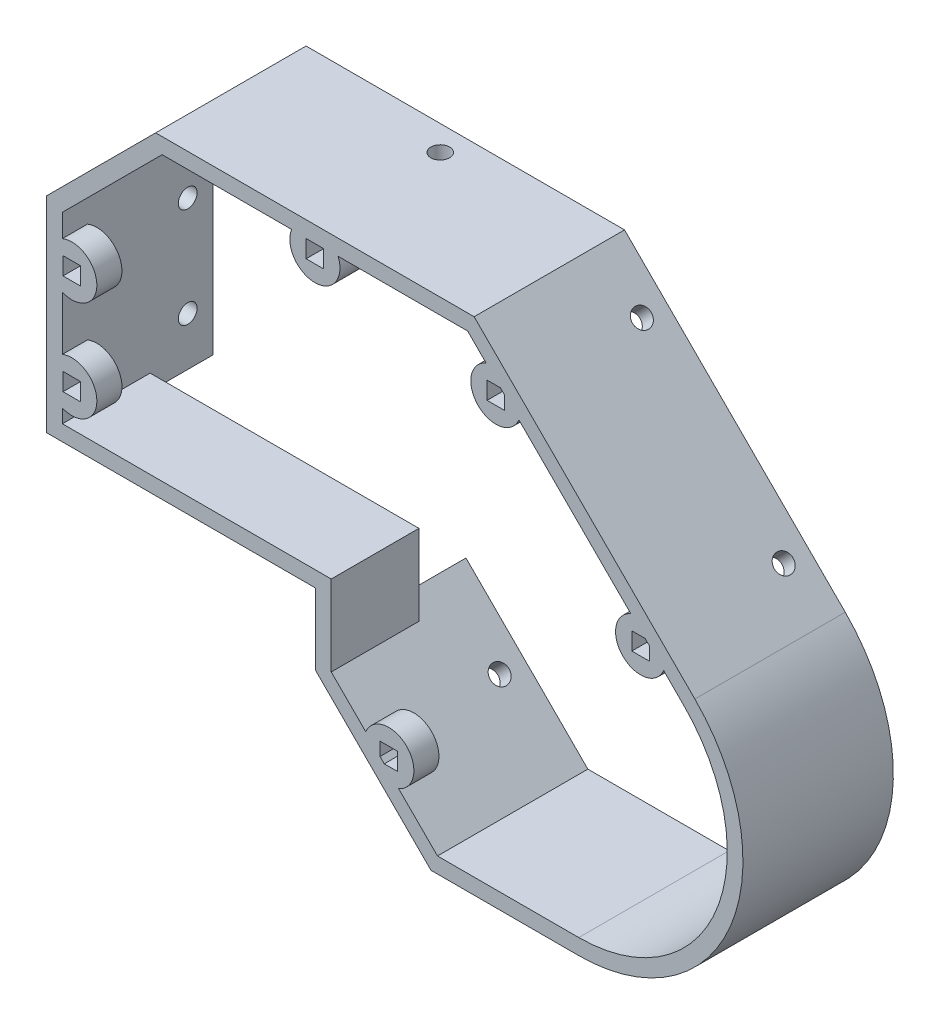
SolidWorks part; units mm, degrees
ref_plane "Plano frontal" through (0, 0, 0) normal (0, 0, 1) x (1, 0, 0)
ref_plane "Plano superior" through (0, 0, 0) normal (0, 1, 0) x (1, 0, 0)
ref_plane "Plano direito" through (0, 0, 0) normal (1, 0, 0) x (0, 0, -1)
sketch "Model" plane through (0, 0, 0) normal (0, 0, 1) x (1, 0, 0)
  line L0 (0, 0) -> (39, 0) construction
  line L1 (-0.7, 2.5) -> (39, 2.5)
  line L2 (39.7, 0) -> (39.7, -6.8548) construction
  line L3 (0, 0) -> (0, 31.4419) construction
  line L4 (50.1111, 46.949) -> (15.5071, 46.949) construction
  line L5 (0, 31.4419) -> (15.5071, 46.949) construction
  line L6 (42.2, -9.3548) -> (52.4452, -19.6) construction
  line L7 (39, -7.1448) -> (51.9502, -20.095) construction
  line L8 (97.9635, 12.6635) -> (63.6779, 46.949) construction
  line L9 (50.1111, 46.949) -> (63.6779, 46.949) construction
  line L10 (52.4452, -19.6) -> (59.4452, -26.6) construction
  line L11 (81.7, -26.6) -> (59.4452, -26.6) construction
  line L12 (-0.7, 0) -> (39, 0)
  line L13 (-0.7, 0) -> (-3.2, 0)
  line L14 (42.2, -10.3448) -> (51.9502, -20.095)
  line L15 (51.9502, -20.095) -> (59.1552, -27.3)
  line L16 (81.7, -27.3) -> (59.1552, -27.3)
  line L17 (98.4584, 13.1584) -> (63.9678, 47.649)
  line L18 (50.1111, 47.649) -> (63.9678, 47.649)
  line L19 (50.1111, 47.649) -> (15.2171, 47.649)
  line L20 (-0.7, 31.7319) -> (15.2171, 47.649)
  line L21 (-0.7, 2.5) -> (-0.7, 31.7319)
  line L22 (0, 0) -> (-0.7, 0) construction
  line L23 (38.8515, -10.5318) -> (50.1824, -21.8627) construction
  line L24 (-3.2, 0) -> (-3.2, 5)
  line L25 (-0.7, -0.7) -> (-0.7, 31.7319) construction
  line L26 (-0.7, -0.7) -> (39, -0.7) construction
  line L27 (39, -0.7) -> (39, -7.1448) construction
  line L28 (39, -0.7) -> (39, -0.7) construction
  line L29 (39, 0) -> (39.7, 0)
  line L30 (39.7, 0) -> (39.7, -11.3803)
  line L31 (39, 2.5) -> (39.7, 2.5)
  line L32 (39.7, 2.5) -> (42.2, 2.5)
  line L33 (39, 0) -> (39.7, 0) construction
  line L34 (42.2, 2.5) -> (42.2, -10.3448)
  line L35 (-3.2, 5) -> (-3.2, 32.7674)
  line L36 (-3.2, 32.7674) -> (14.1816, 50.149)
  line L37 (50.1111, 50.149) -> (14.1816, 50.149)
  line L38 (50.1111, 50.149) -> (65.0034, 50.149)
  line L39 (100.2262, 14.9262) -> (65.0034, 50.149)
  line L40 (81.7, -29.8) -> (58.1197, -29.8)
  line L41 (50.1824, -21.8627) -> (58.1197, -29.8)
  line L42 (39.7, -11.3803) -> (50.1824, -21.8627)
  line L43 (-0.7, 2.5) -> (-5.7, 2.5) construction
  line L44 (-5.7, 0) -> (-5.7, 2.5) construction
  line L45 (-0.7, 0) -> (-5.7, 0) construction
  line L46 (-3.2, 5) -> (-8.2, 5) construction
  line L47 (-8.2, -2.5) -> (-8.2, 5) construction
  line L48 (-0.7, -2.5) -> (39, -2.5) construction
  line L49 (-0.7, -2.5) -> (-8.2, -2.5) construction
  line L51 (40.6192, -8.764) -> (51.9502, -20.095) construction
  line L52 (39.7, -6.8548) -> (52.4452, -19.6) construction
  arc A0 (81.7, -27.3) -> (98.4584, 13.1584) centre (81.7, -3.6) ccw
  arc A1 (81.7, -29.8) -> (100.2262, 14.9262) centre (81.7, -3.6) ccw
  circle A2 centre (59.0726, 19.0274) radius 7.35 construction
  arc A5 (81.7, -26.6) -> (97.9635, 12.6635) centre (81.7, -3.6) ccw construction
  circle A6 centre (81.7, -3.6) radius 7.3 construction
  circle A13 centre (27.384, 23.481) radius 7.35 construction
  dimension "D2" = 2.5
  dimension "D1" = 0.7
extrude "Ressalto-extrusão1" add sketch "Model" along normal blind 48
sketch "Esboço12" plane through (57.5762, 57.5762, 0) normal (0.7071, 0.7071, 0) x (0, 0, -1)
  line L0 (-48, -35.4099) -> (-44, -35.4099) construction
  line L1 (-48, -60.3162) -> (-48, -10.5036) construction
  line L2 (-44, -35.4099) -> (-44, -43.4099) construction
  line L7 (-45.4, -52.0727) -> (-44, -52.0727) construction
  line L9 (-45.4, -20.0727) -> (-44, -20.0727) construction
  circle A0 centre (-44, -20.0727) radius 1.5
  circle A1 centre (-44, -52.0727) radius 1.5
extrude "Corte-extrusão10" cut sketch "Esboço12" against normal blind 10
sketch "Esboço13" plane through (0, 50.149, 0) normal (0, 1, 0) x (1, 0, 0)
  line L0 (39.5925, -48) -> (39.5925, -44) construction
  line L1 (65.0034, -48) -> (14.1816, -48) construction
  circle A0 centre (39.5925, -44) radius 1.5
extrude "Corte-extrusão11" cut sketch "Esboço13" against normal blind 10
sketch "Esboço14" plane through (-3.2, 0, 0) normal (-1, 0, 0) x (0, 0, 1)
  line L0 (48, 16.3837) -> (44, 16.3837) construction
  line L1 (48, 32.7674) -> (48, 0) construction
  line L2 (45.3801, 22.301) -> (45.3801, 25.101) construction
  line L3 (45.3626, 6.3583) -> (45.3626, 9.1235) construction
  line L4 (45.3801, 22.301) -> (45.3801, 25.101) construction
  line L5 (45.3626, 6.3583) -> (45.3626, 9.1235) construction
  line L6 (45.3801, 23.701) -> (44, 23.701) construction
  line L7 (45.3626, 7.7409) -> (44, 7.7409) construction
  circle A0 centre (44, 23.701) radius 1.5
  circle A1 centre (44, 7.7409) radius 1.5
extrude "Corte-extrusão12" cut sketch "Esboço14" against normal blind 10
sketch "Esboço15" plane through (14.1598, 14.1598, 0) normal (-0.7071, -0.7071, 0) x (0, 0, 1)
  line L0 (48, -62.1686) -> (44, -62.1686) construction
  line L1 (48, -62.1686) -> (0, -62.1686) construction
  line L2 (0, -36.4548) -> (0, -50.9436) construction
  line L3 (0, -50.9436) -> (0, -60.8431) construction
  line L4 (0, -36.4548) -> (0, -50.9436) construction
  line L5 (0, -50.9436) -> (0, -60.8431) construction
  line L6 (0, -60.8431) -> (0, -36.4548) construction
  line L7 (0, -36.4548) -> (0, -48.6489) construction
  line L8 (0, -48.6489) -> (48, -48.6489) construction
  line L9 (48, -36.1192) -> (48, -62.1686) construction
  line L11 (45.4, -48.2812) -> (45.4, -45.4812) construction
  line L12 (45.4, -48.2812) -> (45.4, -45.4812) construction
  line L13 (45.4, -46.8812) -> (44, -46.8812) construction
  circle A0 centre (44, -46.8812) radius 1.5
extrude "Corte-extrusão13" cut sketch "Esboço15" against normal blind 10
sketch "Esboço16" plane through (0, 0, 48) normal (0, 0, 1) x (1, 0, 0)
  line L0 (39.7, 0) -> (39.7, -7.8448)
  line L3 (42.2, -10.3448) -> (39.7, -7.8448)
  line L4 (42.2, -10.3448) -> (42.2, 2.5)
  line L5 (42.2, 2.5) -> (-0.7, 2.5)
  line L6 (39.7, 0) -> (39.7, -7.8448) construction
  line L12 (-0.7, 0) -> (39.7, 0)
  line L13 (-0.7, 2.5) -> (-0.7, 0)
extrude "Corte-extrusão14" cut sketch "Esboço16" against normal blind 10
sketch "Esboço18" plane through (0, 0, 0) normal (0, 0, -1) x (-1, 0, 0)
  line L8 (-39.7, 0) -> (3.2, 0)
  line L9 (3.2, 0) -> (3.2, 32.7674)
  line L10 (3.2, 32.7674) -> (-14.1816, 50.149)
  line L11 (-14.1816, 50.149) -> (-65.0034, 50.149)
  line L12 (-65.0034, 50.149) -> (-100.2262, 14.9262)
  line L13 (-81.7, -29.8) -> (-58.1197, -29.8)
  line L14 (-58.1197, -29.8) -> (-39.7, -11.3803)
  line L15 (-39.7, -11.3803) -> (-39.7, 0)
  line L16 (-39.7, 0) -> (3.2, 0)
  line L17 (3.2, 0) -> (3.2, 32.7674)
  line L18 (3.2, 32.7674) -> (-14.1816, 50.149)
  line L19 (-14.1816, 50.149) -> (-65.0034, 50.149)
  line L20 (-65.0034, 50.149) -> (-100.2262, 14.9262)
  line L21 (-81.7, -29.8) -> (-58.1197, -29.8)
  line L22 (-58.1197, -29.8) -> (-39.7, -11.3803)
  line L23 (-39.7, -11.3803) -> (-39.7, 0)
  arc A1 (-100.2262, 14.9262) -> (-81.7, -29.8) centre (-81.7, -3.6) ccw
  arc A2 (-100.2262, 14.9262) -> (-81.7, -29.8) centre (-81.7, -3.6) ccw
  dimension "D1" = 0
extrude "Corte-extrusão15" cut sketch "Esboço18" against normal blind 24
sketch "Esboço17" plane through (0, 0, 24) normal (0, 0, -1) x (-1, 0, 0)
  line L0 (-93.3365, 21.8159) -> (-95.4578, 19.6946) construction
  line L1 (-93.3365, 21.8159) -> (-95.4578, 19.6946) construction
  line L2 (-70.709, 44.4433) -> (-72.8304, 42.322) construction
  line L3 (-70.709, 44.4433) -> (-72.8304, 42.322) construction
  line L4 (-38.0925, 50.149) -> (-41.0925, 50.149) construction
  line L5 (-38.0925, 50.149) -> (-41.0925, 50.149) construction
  line L6 (3.2, 22.201) -> (3.2, 25.201) construction
  line L7 (3.2, 22.201) -> (3.2, 25.201) construction
  line L8 (3.2, 6.2409) -> (3.2, 9.2409) construction
  line L9 (3.2, 6.2409) -> (3.2, 9.2409) construction
  line L10 (-48.3705, -20.0508) -> (-46.2492, -17.9295) construction
  line L11 (-48.3705, -20.0508) -> (-46.2492, -17.9295) construction
  line L12 (-94.3971, 20.7553) -> (-91.5687, 17.9268) construction
  line L14 (-39.5925, 50.149) -> (-39.5925, 46.149) construction
  line L18 (-69.8727, 39.6229) -> (-67.0727, 39.6229)
  line L19 (-92.9687, 19.3268) -> (-90.1687, 19.3268)
  line L20 (-92.9687, 19.3268) -> (-92.9687, 16.5268)
  line L21 (-92.9687, 16.5268) -> (-90.1687, 16.5268)
  line L22 (-90.1687, 19.3268) -> (-90.1687, 16.5268)
  line L23 (-92.9687, 19.3268) -> (-90.1687, 16.5268) construction
  line L24 (-92.9687, 16.5268) -> (-90.1687, 19.3268) construction
  line L25 (-69.8727, 39.6229) -> (-67.0727, 42.4229) construction
  line L26 (-69.8727, 42.4229) -> (-67.0727, 39.6229) construction
  line L27 (-69.8727, 42.4229) -> (-69.8727, 39.6229)
  line L28 (-69.8727, 42.4229) -> (-67.0727, 42.4229)
  line L29 (-67.0727, 42.4229) -> (-67.0727, 39.6229)
  line L30 (-38.1925, 47.549) -> (-38.1925, 44.749)
  line L31 (-40.9925, 44.749) -> (-38.1925, 47.549) construction
  line L32 (-40.9925, 47.549) -> (-40.9925, 44.749)
  line L33 (-40.9925, 47.549) -> (-38.1925, 44.749) construction
  line L34 (-40.9925, 44.749) -> (-38.1925, 44.749)
  line L35 (-40.9925, 47.549) -> (-38.1925, 47.549)
  line L36 (-2.2, 25.7837) -> (0.6, 22.9837) construction
  line L37 (-2.2, 22.9837) -> (0.6, 22.9837)
  line L38 (0.6, 25.7837) -> (0.6, 22.9837)
  line L39 (-2.2, 25.7837) -> (0.6, 25.7837)
  line L40 (-2.2, 22.9837) -> (0.6, 25.7837) construction
  line L41 (-2.2, 25.7837) -> (-2.2, 22.9837)
  line L42 (0.6, 9.7837) -> (0.6, 6.9837)
  line L43 (-2.2, 9.7837) -> (0.6, 9.7837)
  line L44 (-2.2, 6.9837) -> (0.6, 6.9837)
  line L45 (-2.2, 9.7837) -> (0.6, 6.9837) construction
  line L46 (-2.2, 9.7837) -> (-2.2, 6.9837)
  line L47 (-2.2, 6.9837) -> (0.6, 9.7837) construction
  line L48 (-52.7883, -18.8117) -> (-49.9883, -18.8117)
  line L49 (-52.7883, -16.0117) -> (-49.9883, -18.8117) construction
  line L50 (-52.7883, -18.8117) -> (-49.9883, -16.0117) construction
  line L51 (-52.7883, -16.0117) -> (-49.9883, -16.0117)
  line L52 (-49.9883, -16.0117) -> (-49.9883, -18.8117)
  line L53 (-52.7883, -16.0117) -> (-52.7883, -18.8117)
  circle A0 centre (-91.5687, 17.9268) radius 4
  circle A1 centre (-68.4727, 41.0229) radius 4
  circle A2 centre (-39.5925, 46.149) radius 4
  circle A3 centre (-0.8, 24.3837) radius 4
  circle A4 centre (-0.8, 8.3837) radius 4
  circle A5 centre (-51.3883, -17.4117) radius 4
extrude "Ressalto-extrusão2" add sketch "Esboço17" against normal blind 4
mirror "Espelhar2" about plane through (81.7, -3.6, 48) normal (0, 0, 1) of bodies 116
sketch "Esboço19" plane through (0, 0, 24) normal (0, 0, -1) x (-1, 0, 0)
  line L8 (-58.1197, -29.8) -> (-39.7, -11.3803)
  line L9 (-39.7, -11.3803) -> (-39.7, 0)
  line L10 (-39.7, 0) -> (3.2, 0)
  line L11 (3.2, 0) -> (3.2, 32.7674)
  line L12 (3.2, 32.7674) -> (-14.1816, 50.149)
  line L13 (-14.1816, 50.149) -> (-65.0034, 50.149)
  line L14 (-65.0034, 50.149) -> (-100.2262, 14.9262)
  line L15 (-81.7, -29.8) -> (-58.1197, -29.8)
  line L16 (-58.1197, -29.8) -> (-39.7, -11.3803)
  line L17 (-39.7, -11.3803) -> (-39.7, 0)
  line L18 (-39.7, 0) -> (3.2, 0)
  line L19 (3.2, 0) -> (3.2, 32.7674)
  line L20 (3.2, 32.7674) -> (-14.1816, 50.149)
  line L21 (-14.1816, 50.149) -> (-65.0034, 50.149)
  line L22 (-65.0034, 50.149) -> (-100.2262, 14.9262)
  line L23 (-81.7, -29.8) -> (-58.1197, -29.8)
  arc A1 (-100.2262, 14.9262) -> (-81.7, -29.8) centre (-81.7, -3.6) ccw
  arc A2 (-100.2262, 14.9262) -> (-81.7, -29.8) centre (-81.7, -3.6) ccw
  dimension "D1" = 0
extrude "Corte-extrusão16" cut sketch "Esboço19" against normal blind 24
